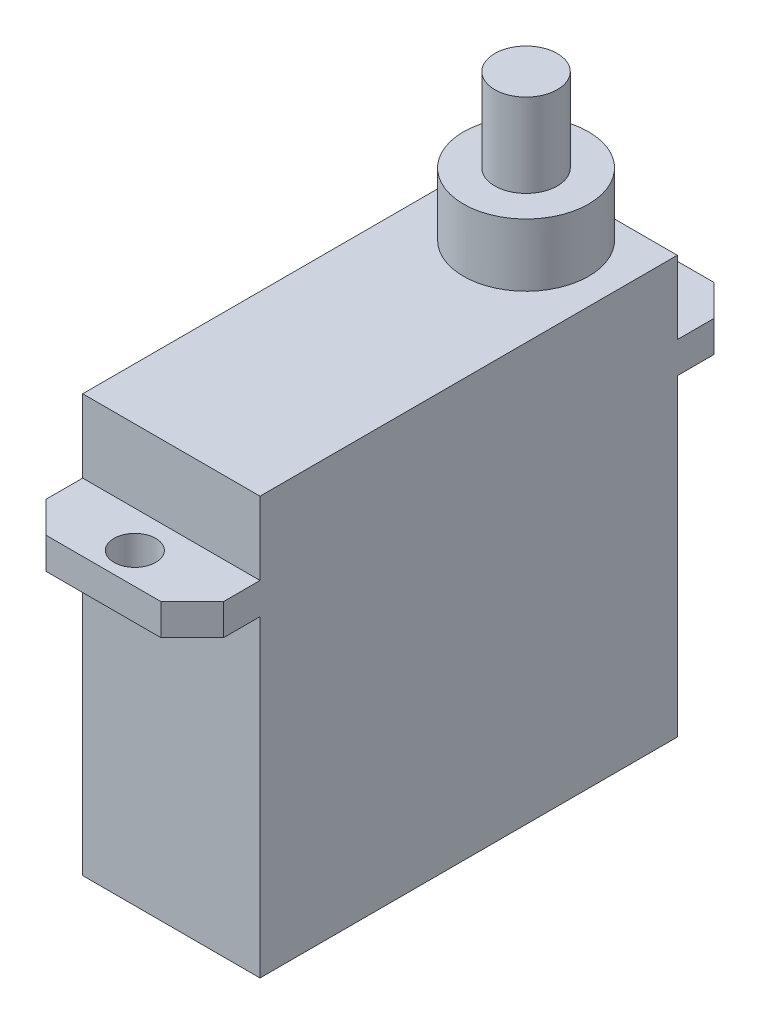
SolidWorks part; units mm, degrees
ref_plane "Front Plane" through (0, 0, 0) normal (0, 0, 1) x (1, 0, 0)
ref_plane "Top Plane" through (0, 0, 0) normal (0, 1, 0) x (1, 0, 0)
ref_plane "Right Plane" through (0, 0, 0) normal (1, 0, 0) x (0, 0, -1)
sketch "Sketch1" plane through (0, 0, 0) normal (0, 1, 0) x (1, 0, 0)
  line L1 (-4.25, -10) -> (4.25, -10)
  line L2 (-4.25, -10) -> (-4.25, 10)
  line L3 (-4.25, 10) -> (4.25, 10)
  line L4 (4.25, -10) -> (4.25, 10)
  line L5 (-4.25, -10) -> (4.25, 10) construction
  line L6 (-4.25, 10) -> (4.25, -10) construction
  point P0 (0, 0)
  dimension "D1" = 8.5
  dimension "D2" = 20
extrude "Boss-Extrude1" add sketch "Sketch1" along normal blind 20
ref_plane "Plane1" through (0, 15, 0) normal (0, 1, 0) x (1, 0, 0)
sketch "Sketch4" plane through (0, 15, 0) normal (0, 1, 0) x (1, 0, 0)
  line L0 (-10.2578, 0) -> (10.2578, 0) construction
  line L1 (-4.25, 10) -> (4.25, 10)
  line L2 (-4.25, 10) -> (-4.25, 11.75)
  line L3 (-2.75, 13.25) -> (2.75, 13.25)
  line L4 (4.25, 10) -> (4.25, 11.75)
  line L5 (-4.25, 11.75) -> (-2.75, 13.25)
  line L6 (2.75, 13.25) -> (4.25, 11.75)
  line L7 (-2.75, -13.25) -> (2.75, -13.25)
  line L8 (2.75, -13.25) -> (4.25, -11.75)
  line L9 (4.25, -10) -> (4.25, -11.75)
  line L10 (-4.25, -10) -> (4.25, -10)
  line L11 (-4.25, -11.75) -> (-2.75, -13.25)
  line L12 (-4.25, -10) -> (-4.25, -11.75)
  circle A0 centre (0, 11.75) radius 1
  circle A1 centre (0, -11.75) radius 1
  point P1 (4.25, 13.25)
  point P2 (-4.25, 13.25)
  point P10 (0, 0)
  dimension "D2" = 2
  dimension "D1" = 11.75
  dimension "D3" = 3.25
extrude "Boss-Extrude2" add sketch "Sketch4" along normal blind 1.5
sketch "Sketch6" plane through (0, 20, 0) normal (0, 1, 0) x (1, 0, 0)
  line L0 (4.25, 10) -> (-4.25, 10) construction
  circle A0 centre (0, 7) radius 3
  dimension "D1" = 6
extrude "Boss-Extrude3" add sketch "Sketch6" along normal blind 3
sketch "Sketch7" plane through (0, 23, 0) normal (0, 1, 0) x (1, 0, 0)
  circle A0 centre (0, 7) radius 1.5
  dimension "D1" = 3
extrude "Boss-Extrude4" add sketch "Sketch7" along normal blind 4
